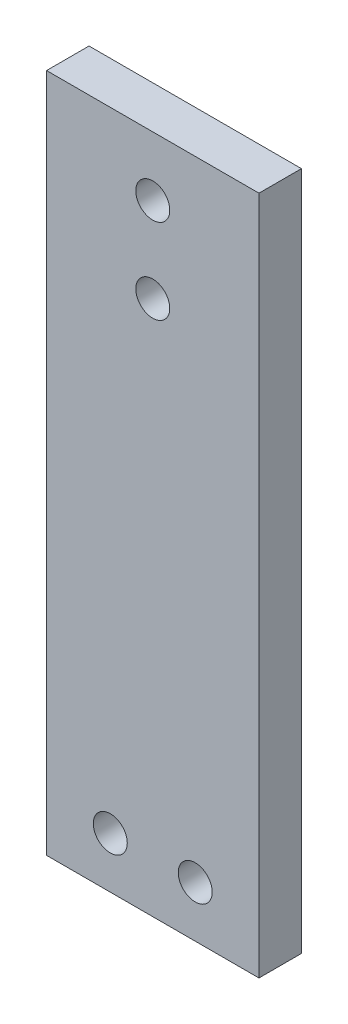
SolidWorks part; units mm, degrees
ref_plane "前视基准面" through (0, 0, 0) normal (0, 0, 1) x (1, 0, 0)
ref_plane "上视基准面" through (0, 0, 0) normal (0, 1, 0) x (1, 0, 0)
ref_plane "右视基准面" through (0, 0, 0) normal (1, 0, 0) x (0, 0, -1)
other "Configuration Table"
sketch "草图1" plane through (0, 0, 0) normal (0, 0, 1) x (1, 0, 0)
  line L1 (-12.5, 40) -> (12.5, 40)
  line L2 (-12.5, 40) -> (-12.5, -40)
  line L3 (-12.5, -40) -> (12.5, -40)
  line L4 (12.5, 40) -> (12.5, -40)
  line L5 (-12.5, 40) -> (12.5, -40) construction
  line L6 (-12.5, -40) -> (12.5, 40) construction
  point P0 (0, 0)
  dimension "D1" = 25
  dimension "D2" = 80
extrude "凸台-拉伸1" add sketch "草图1" against normal blind 5
sketch "草图2" plane through (0, 0, 0) normal (0, 0, 1) x (1, 0, 0)
  line L0 (-12.5, 33) -> (12.5, 33) construction
  line L1 (-12.5, 40) -> (-12.5, -40) construction
  line L2 (12.5, -40) -> (12.5, 40) construction
  line L3 (-12.5, 23) -> (12.5, 23) construction
  line L4 (-12.5, -34) -> (12.5, -34) construction
  line L5 (0, 40) -> (0, -40) construction
  line L6 (12.5, 40) -> (-12.5, 40) construction
  line L7 (-12.5, -40) -> (12.5, -40) construction
  line L8 (-5, 40) -> (-5, -40) construction
  line L9 (5, 40) -> (5, -40) construction
  circle A0 centre (0, 33) radius 2
  circle A1 centre (0, 23) radius 2
  circle A2 centre (-5, -34) radius 2
  circle A3 centre (5, -34) radius 2
  point P8 (0, 23)
  point P9 (0, 40)
  point P16 (0, 33)
  point P27 (-5, -34)
  point P28 (5, -34)
  dimension "D3" = 4
  dimension "D7" = 4
  dimension "D1" = 7
  dimension "D2" = 10
  dimension "D4" = 6
  dimension "D5" = 10
  dimension "D6" = 7.5
extrude "切除-拉伸1" cut sketch "草图2" against normal through all
